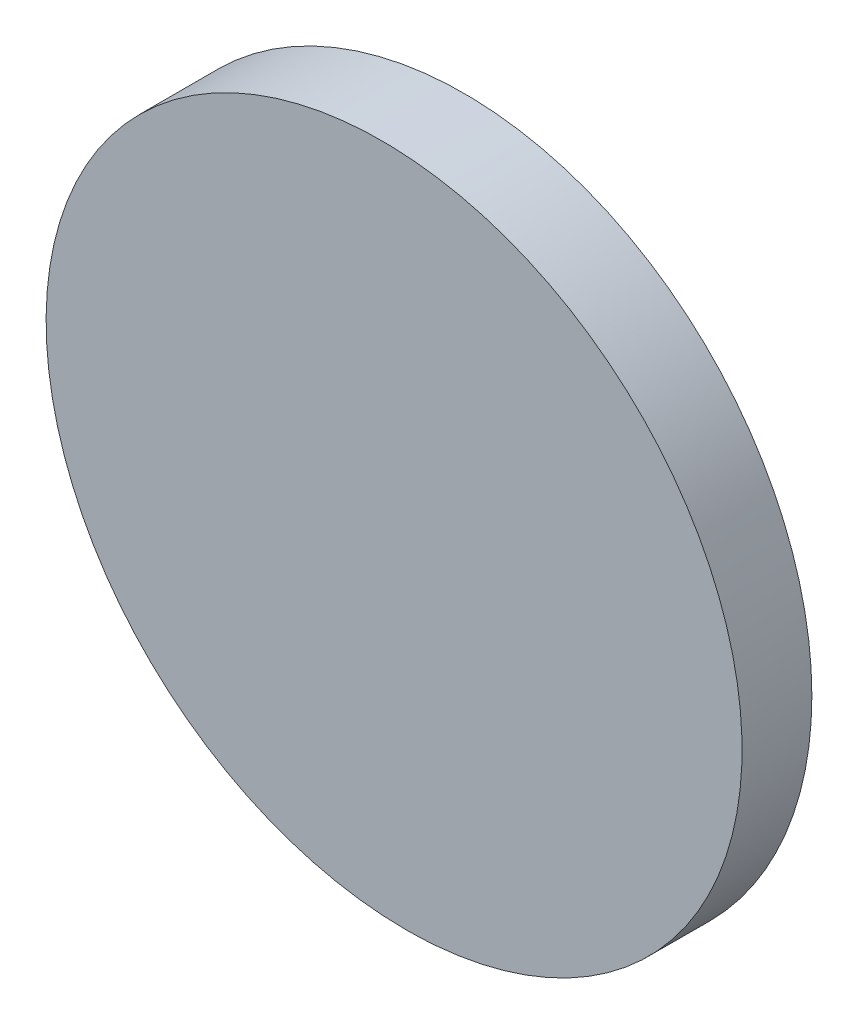
SolidWorks part; units mm, degrees
ref_plane "前视基准面" through (0, 0, 0) normal (0, 0, 1) x (1, 0, 0)
ref_plane "上视基准面" through (0, 0, 0) normal (0, 1, 0) x (1, 0, 0)
ref_plane "右视基准面" through (0, 0, 0) normal (1, 0, 0) x (0, 0, -1)
sketch "草图2" plane through (0, 0, 0) normal (0, 0, 1) x (1, 0, 0)
  circle A0 centre (0, 0) radius 25.4
  dimension "D1" = 50.8
extrude "凸台-拉伸1" add sketch "草图2" along normal blind 6
sketch "草图3" plane through (0, 0, 0) normal (1, 0, 0) x (0, 0, -1)
  line L0 (-6, -25.4317) -> (-4.2249, -25.4317)
  line L1 (-4.2249, -25.4317) -> (-6, 25.4)
  line L2 (-6, 25.4) -> (-6, -25.4) construction
  line L3 (-6, -25.4317) -> (-6, 25.4)
  dimension "D1" = 50.8317
  dimension "D2" = 50.8627
  dimension "D3" = 88
extrude "切除-拉伸1" cut sketch "草图3" against normal mid plane 100
